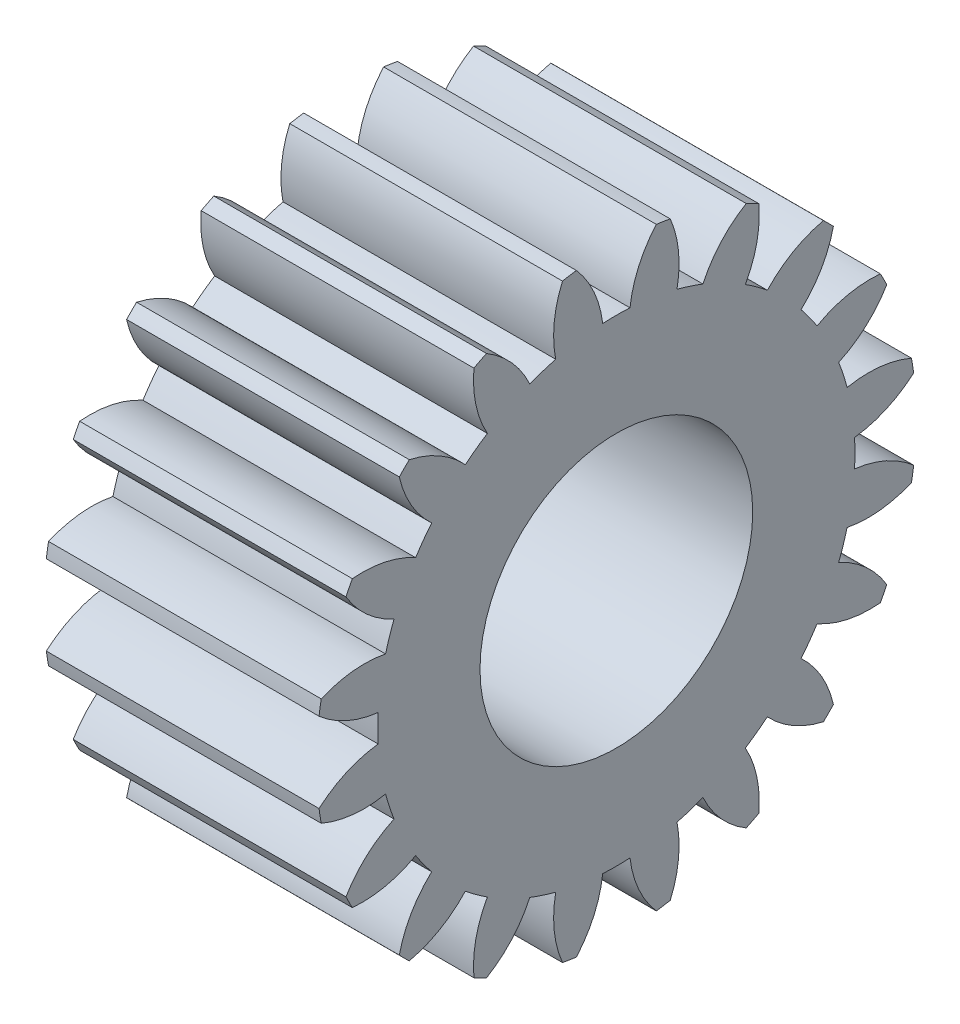
SolidWorks part; units mm, degrees
ref_plane "Plane1" through (0, 0, 0) normal (0, 0, 1) x (1, 0, 0)
ref_plane "Plane2" through (0, 0, 0) normal (0, 1, 0) x (1, 0, 0)
ref_plane "Plane3" through (0, 0, 0) normal (1, 0, 0) x (0, 0, -1)
other "Configuration Table"
sketch "HoldingSke" plane through (0, 0, 0) normal (0, 1, 0) x (1, 0, 0)
  line L0 (0, 0) -> (0.9397, -0.342)
  line L1 (-15, 0) -> (100, 0) construction
  line L2 (0, 0) -> (-2.1039, 2.3779)
  line L3 (0, 0) -> (-11.863, 4.5341)
  line L4 (0, 0) -> (8.1152, 2.9537)
  line L5 (0, 0) -> (-46.8476, -17.4728)
  line L6 (0, 0) -> (-8.2896, -5.593)
  line L7 (-2.1039, 2.3779) -> (8.6586, 51.2059)
  line L8 (-76.2, 54.61) -> (-74.4, 54.61)
  line L9 (-71.009, 38.7566) -> (-53.1078, 45.2721)
  line L10 (-76.2, 71.12) -> (104.1128, 71.12)
  line L11 (0, 0) -> (-10, 0)
  line L12 (-76.2, 101.6) -> (-76.162, 101.6)
  line L13 (24.9733, 27.94) -> (52.9518, 28.4284)
  line L14 (24.9733, 27.94) -> (24.9743, 27.94)
  line L15 (24.9733, 27.94) -> (100.4006, 29.5858)
  line L16 (-63.627, -1) -> (-12.827, -1)
  circle A0 centre (0, 0) radius 5
  circle A1 centre (0, 0) radius 8.749
  circle A2 centre (0, 0) radius 37.5
  circle A3 centre (0, 0) radius 5
  dimension "MHD" = 17.498
  dimension "Hub_dia" = 75
  dimension "Bore" = 10
  dimension "MBD" = 10
  dimension "Num_teeth" = 20
  dimension "Pitch" = 1
  dimension "Overall_len" = 50
  dimension "Show_teeth" = 20
  dimension "Thickness" = 10
  dimension "OAL" = 50.0001
  dimension "T_dim" = 1.8
  dimension "Ap" = 20
  dimension "H" = 19.05
  dimension "Pitch_radius" = 180.3128
  dimension "Width" = 10
  dimension "Backlash" = 0.038
  dimension "Addendum_fac" = 1
  dimension "Dedendum_fac" = 1.25
  dimension "Clearance_fac" = 0.25
  dimension "Dedendum_add" = 0.001
  dimension "Module" = 1
sketch "BasProSke" plane through (0, 0, 0) normal (0, 1, 0) x (1, 0, 0)
  line L0 (-10, 0) -> (60, 0) construction
  line L1 (0, 0) -> (0, 11)
  line L2 (0, 0) -> (10, 0)
  line L3 (10, 0) -> (10, 11)
  line L4 (10, 11) -> (0, 11)
  dimension "Thickness" = 10
  dimension "Diameter" = 22
revolve "Base-Revolve" add sketch "BasProSke" angle 360 about L0
sketch "TooCutSke" plane through (0, 0, 0) normal (1, 0, 0) x (0, 0, -1)
  line L1 (0, 0) -> (0, 107) construction
  line L2 (0, 0) -> (-0.8511, 9.9637) construction
  line L3 (0, 0) -> (-3.1206, 19.7028) construction
  line L4 (-0.8511, 9.9637) -> (-1.5603, 9.8514) construction
  arc A0 (0.4999, 8.7347) -> (-0.4999, 8.7347) centre (0, 0) ccw
  arc A1 (1.4852, 10.9249) -> (-1.4852, 10.9249) centre (0, 0) ccw
  circle A2 centre (0, 0) radius 10 construction
  circle A3 centre (0, 0) radius 9.3969 construction
  arc A4 (-0.4999, 8.7347) -> (-1.4852, 10.9249) centre (-4.4722, 8.2645) ccw
  arc A5 (1.4852, 10.9249) -> (0.4999, 8.7347) centre (4.4722, 8.2645) ccw
  dimension "Root_dia" = 17.498
  dimension "Overcut_dia" = 22.0508
  dimension "Pitch_dia" = 20
  dimension "Base_dia" = 18.7939
  dimension "Flank_rad" = 4
  dimension "Half_ang" = 9
  dimension "Half_CT" = 0.7181
extrude "ToothCut" cut sketch "TooCutSke" along normal through all
fillet "Breaks" [suppressed] radius 0.02
fillet "RootFillets" [suppressed] radius 0.251
pattern_circular "TeethCuts" count 20 every 18 about axis through (-10, 0, 0) along (1, 0, 0) of "ToothCut", "RootFillets", "Breaks"
sketch "HubNeaOneSke" plane through (0, 0, 0) normal (-1, 0, 0) x (0, 0, 1)
  circle A0 centre (0, 0) radius 8.749
  dimension "Diameter" = 17.498
extrude "HubNearOne" [suppressed] add sketch "HubNeaOneSke" along normal blind 40.0001
sketch "HubNeaBotSke" plane through (0, 0, 0) normal (-1, 0, 0) x (0, 0, 1)
  circle A0 centre (0, 0) radius 8.749
  dimension "Diameter" = 17.498
extrude "HubNearBoth" [suppressed] add sketch "HubNeaBotSke" along normal blind 20
ref_plane "FarPln" through (10, 0, 0) normal (1, 0, 0) x (0, 0, -1)
sketch "HubFarSke" plane through (10, 0, 0) normal (1, 0, 0) x (0, 0, -1)
  circle A0 centre (0, 0) radius 8.749
  dimension "Diameter" = 17.498
extrude "HubFar" [suppressed] add sketch "HubFarSke" along normal blind 20
sketch "BorSke" plane through (0, 0, 0) normal (1, 0, 0) x (0, 0, -1)
  circle A0 centre (0, 0) radius 5
  dimension "Diameter" = 10
extrude "Bore" cut sketch "BorSke" along normal mid plane 100.0001
sketch "KeySke" plane through (0, 0, 0) normal (1, 0, 0) x (0, 0, -1)
  line L0 (-2, 0) -> (-2, 6.8)
  line L1 (-2, 6.8) -> (2, 6.8)
  line L2 (2, 6.8) -> (2, 0)
  line L3 (0, 0) -> (0, 34) construction
  line L4 (-2, 0) -> (2, 0)
  dimension "Offset" = 6.8
  dimension "Width" = 4
extrude "Keyway" [suppressed] cut sketch "KeySke" along normal mid plane 100.0001
pattern_circular "Keyway2" [suppressed] count 2 every 90 about axis through (-10, 0, 0) along (1, 0, 0)
equation "' \"Module@HoldingSke\" = 6.35"
equation "' \"Num_teeth@HoldingSke\" = 12"
equation "' \"Ap@HoldingSke\" =  20"
equation "' \"Ap@HoldingSke\" = 20"
equation "' \"Width@HoldingSke\" = 0.5 * 25.4"
equation "' \"Hub_dia@HoldingSke\"= 1 * 25.4"
equation "' \"Hub_dia@HoldingSke\" = 1 * 25.4"
equation "' \"Overall_len@HoldingSke\" = 1.0 * 25.4"
equation "' \"Bore@HoldingSke\" = 0.75 * 25.4"
equation "' \"T_dim@HoldingSke\" = 0.1 * 25.4"
equation "' \"Width@KeySke\" = 0.25 * 25.4"
equation "' \"Show_teeth@HoldingSke\" = 13"
equation "' \"Backlash@HoldingSke\" = 0.009 * 25.4"
equation "' \"Addendum_fac@HoldingSke\" = 1.0"
equation "' \"Dedendum_fac@HoldingSke\" = 1.25"
equation "' \"Dedendum_add@HoldingSke\" = 0.00005 * 25.4"
equation "' \"Clearance_fac@HoldingSke\" = 0.25"
equation "\"Pitch@HoldingSke\" = 1 / \"Module@HoldingSke\""
equation "\"Overcut_dia@TooCutSke\" = (\"Num_teeth@HoldingSke\" + 2 * \"Addendum_fac@HoldingSke\") / \"Pitch@HoldingSke\" + 0.002 * 25.4"
equation "\"Pitch_dia@TooCutSke\" = \"Num_teeth@HoldingSke\" / \"Pitch@HoldingSke\""
equation "\"Base_dia@TooCutSke\" = \"Num_teeth@HoldingSke\" / \"Pitch@HoldingSke\" * cos((\"Ap@HoldingSke\"  * 3.14159265 / 180))"
equation "\"Root_dia@TooCutSke\" = (\"Num_teeth@HoldingSke\" + 2) / \"Pitch@HoldingSke\" - 2 * (\"Addendum_fac@HoldingSke\" + \"Dedendum_fac@HoldingSke\") / \"Pitch@HoldingSke\" - \"Dedendum_add@HoldingSke\" * 2"
equation "\"Half_ang@TooCutSke\" = 180 / \"Num_teeth@HoldingSke\""
equation "\"Half_CT@TooCutSke\" = \"Num_teeth@HoldingSke\" / \"Pitch@HoldingSke\" * sin((3.14159265 / 2 / \"Num_teeth@HoldingSke\")) / 2 - 7 * \"Backlash@HoldingSke\" / 4"
equation "\"Flank_rad@TooCutSke\" = \"Num_teeth@HoldingSke\" / \"Pitch@HoldingSke\" / 5"
equation "\"Radius@RootFillets\" = \"Clearance_fac@HoldingSke\" / \"Pitch@HoldingSke\" + \"Dedendum_add@HoldingSke\""
equation "\"Break_rad@Breaks\" = 0.02 / \"Pitch@HoldingSke\""
equation "\"Thickness@HoldingSke\" = \"Width@HoldingSke\""
equation "\"OAL@HoldingSke\" = \"Thickness@HoldingSke\""
equation "\"MHD@HoldingSke\" = (\"Num_teeth@HoldingSke\" + 2) / \"Pitch@HoldingSke\" - 2 * (\"Addendum_fac@HoldingSke\" + \"Dedendum_fac@HoldingSke\")  / \"Pitch@HoldingSke\" - \"Dedendum_add@HoldingSke\" * 2"
equation "\"MBD@HoldingSke\" = (\"Num_teeth@HoldingSke\" + 2) / \"Pitch@HoldingSke\" - 2 * (\"Addendum_fac@HoldingSke\" + \"Dedendum_fac@HoldingSke\")  / \"Pitch@HoldingSke\" - \"Dedendum_add@HoldingSke\" * 2 - 0.002 * 25.4"
equation "\"MHD@HoldingSke\" = ((sgn( \"MHD@HoldingSke\" - \"Hub_dia@HoldingSke\" )-1)*( \"MHD@HoldingSke\" - \"Hub_dia@HoldingSke\" ))/-2+ \"Hub_dia@HoldingSke\""
equation "\"MBD@HoldingSke\" = ((sgn( \"MBD@HoldingSke\" - \"Bore@HoldingSke\" )-1)*( \"MBD@HoldingSke\" - \"Bore@HoldingSke\" ))/-2+ \"Bore@HoldingSke\""
equation "\"OAL@HoldingSke\" = ((sgn( \"OAL@HoldingSke\" - \"Overall_len@HoldingSke\" )+1)*( \"OAL@HoldingSke\" - \"Overall_len@HoldingSke\" ))/2 + \"Overall_len@HoldingSke\" + 0.000002 * 25.4"
equation "\"Num_teeth@TeethCuts\" = int( \"Show_teeth@HoldingSke\" ) + 1"
equation "\"Num_teeth@TeethCuts\" = ((sgn( \"Num_teeth@TeethCuts\" - \"Num_teeth@HoldingSke\" )-1)*( \"Num_teeth@TeethCuts\" - \"Num_teeth@HoldingSke\" ))/-2+ \"Num_teeth@HoldingSke\""
equation "\"Num_teeth@TeethCuts\" = ((sgn( \"Num_teeth@TeethCuts\" - 2.0)+1)*( \"Num_teeth@TeethCuts\" - 2.0))/2 +2.0"
equation "\"Angle@TeethCuts\" = 360.0 / \"Num_teeth@HoldingSke\""
equation "\"Diameter@BasProSke\" = (\"Num_teeth@HoldingSke\" + 2 * \"Addendum_fac@HoldingSke\") / \"Pitch@HoldingSke\""
equation "\"Thickness@BasProSke\"  = \"Thickness@HoldingSke\""
equation "' \"Fillet_rad@BasProSke\" =  \"Thickness@HoldingSke\" * 0.05"
equation "' \"Fillet_rad@BasProSke\" = \"Thickness@HoldingSke\" * 0.05"
equation "\"MHD@HoldingSke\" = ((sgn( \"MHD@HoldingSke\" - \"Root_dia@TooCutSke\" )-1)*( \"MHD@HoldingSke\" - \"Root_dia@TooCutSke\" ))/-2+ \"Root_dia@TooCutSke\""
equation "\"Diameter@HubNeaOneSke\" = \"MHD@HoldingSke\""
equation "\"Length@HubNearOne\" = \"OAL@HoldingSke\" - \"Thickness@BasProSke\""
equation "\"Diameter@HubNeaBotSke\" = \"MHD@HoldingSke\""
equation "\"Length@HubNearBoth\" = ( \"OAL@HoldingSke\" - \"Thickness@BasProSke\" ) / 2.0"
equation "\"Thickness@FarPln\" = \"Thickness@BasProSke\""
equation "\"Diameter@HubFarSke\" = \"MHD@HoldingSke\""
equation "\"Length@HubFar\" = ( \"OAL@HoldingSke\" - \"Thickness@BasProSke\" ) / 2.0"
equation "\"Diameter@BorSke\" = \"MBD@HoldingSke\""
equation "\"D1@Bore\" = \"OAL@HoldingSke\" * 2.0"
equation "\"D1@Keyway\" = \"OAL@HoldingSke\" * 2.0"
equation "\"Offset@KeySke\" = \"T_dim@HoldingSke\" + \"MBD@HoldingSke\" / 2.0"
